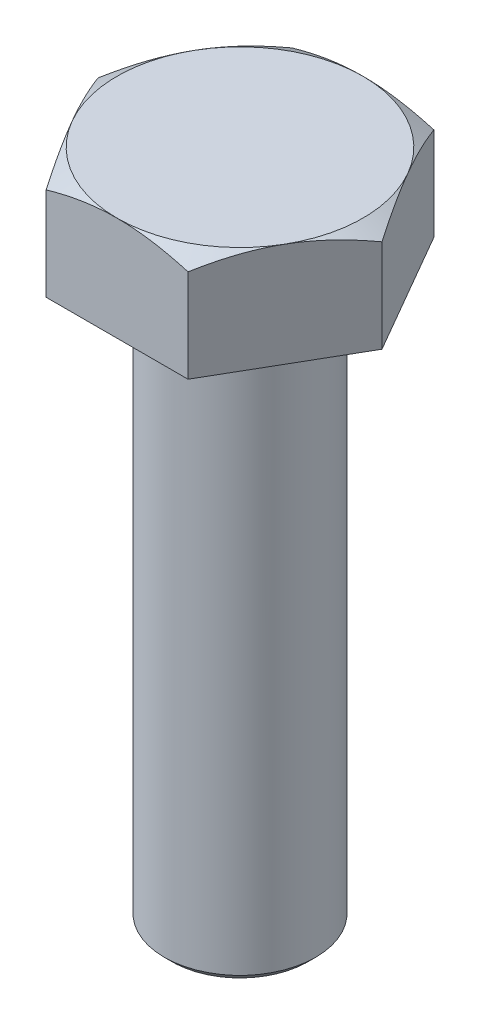
SolidWorks part; units mm, degrees
ref_plane "Front Plane" through (0, 0, 0) normal (0, 0, 1) x (1, 0, 0)
ref_plane "Top Plane" through (0, 0, 0) normal (0, 1, 0) x (1, 0, 0)
ref_plane "Right Plane" through (0, 0, 0) normal (1, 0, 0) x (0, 0, -1)
sketch "Sketch1" plane through (0, 0, 0) normal (0, 1, 0) x (1, 0, 0)
  line L1 (-3.7528, -6.5) -> (3.7528, -6.5)
  line L2 (3.7528, -6.5) -> (7.5056, 0)
  line L3 (7.5056, 0) -> (3.7528, 6.5)
  line L4 (3.7528, 6.5) -> (-3.7528, 6.5)
  line L5 (-3.7528, 6.5) -> (-7.5056, 0)
  line L6 (-7.5056, 0) -> (-3.7528, -6.5)
  circle A0 centre (0, 0) radius 6.5 construction
  dimension "D1" = 13
extrude "Boss-Extrude1" add sketch "Sketch1" along normal blind 5.5
sketch "Sketch2" plane through (0, 0, 0) normal (0, -1, 0) x (1, 0, 0)
  circle A0 centre (0, 0) radius 4
  dimension "D1" = 8
extrude "Boss-Extrude2" add sketch "Sketch2" along normal blind 30
fillet "Fillet1" radius 0.4 1 edges at (0, 0, -4)
chamfer "Chamfer1" distance 0.4 angle 45 1 edges at (0, -30, -4)
sketch "Sketch3" plane through (0, 0, 0) normal (1, 0, 0) x (0, 0, -1)
  line L0 (6.5, 5.5) -> (16.3191, -0.169)
  line L1 (6.5, 5.5) -> (16.3191, 5.5)
  line L4 (16.3191, 5.5) -> (16.3191, -0.169)
  line L5 (0, 0) -> (0, 6.7847) construction
  dimension "D1" = 30
revolve "Cut-Revolve1" cut sketch "Sketch3" angle 360 about L5
